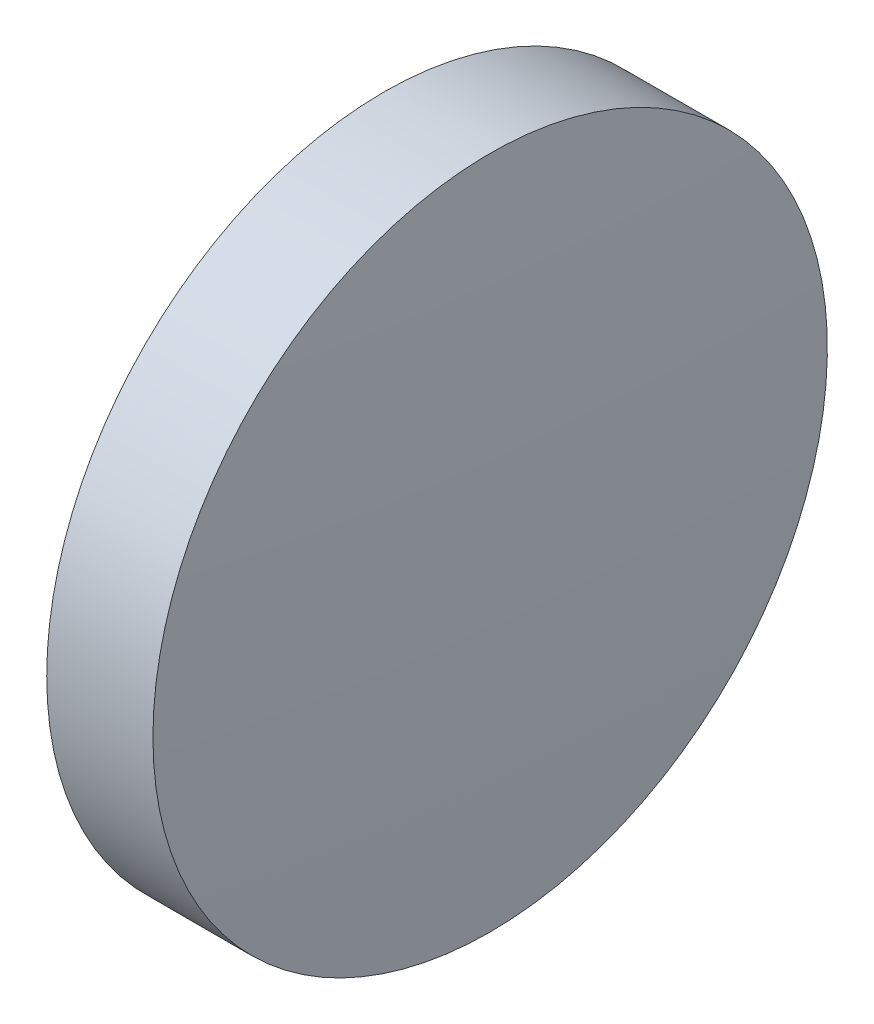
SolidWorks part; units mm, degrees
ref_plane "前视基准面" through (0, 0, 0) normal (0, 0, 1) x (1, 0, 0)
ref_plane "上视基准面" through (0, 0, 0) normal (0, 1, 0) x (1, 0, 0)
ref_plane "右视基准面" through (0, 0, 0) normal (1, 0, 0) x (0, 0, -1)
sketch "草图1" plane through (0, 0, 0) normal (0, 0, 1) x (1, 0, 0)
  line L0 (39.6527, 24.3081) -> (46.7386, 24.3081) construction
  line L1 (42.2291, 30.6581) -> (44.2291, 30.6581)
  line L2 (44.2291, 30.6581) -> (44.2291, 17.9581)
  line L3 (44.2291, 17.9581) -> (42.2291, 17.9581)
  line L4 (42.2291, 17.9581) -> (42.2291, 30.6581)
  arc A0 (42.2291, 30.6581) -> (42.2291, 17.9581) centre (142.9593, 24.3081) ccw
  arc A1 (44.2291, 17.9581) -> (44.2291, 30.6581) centre (-56.5011, 24.3081) ccw
  dimension "D1" = 12.7
  dimension "D2" = 2.0001
revolve "旋转1" add sketch "草图1" angle 360 about L0
